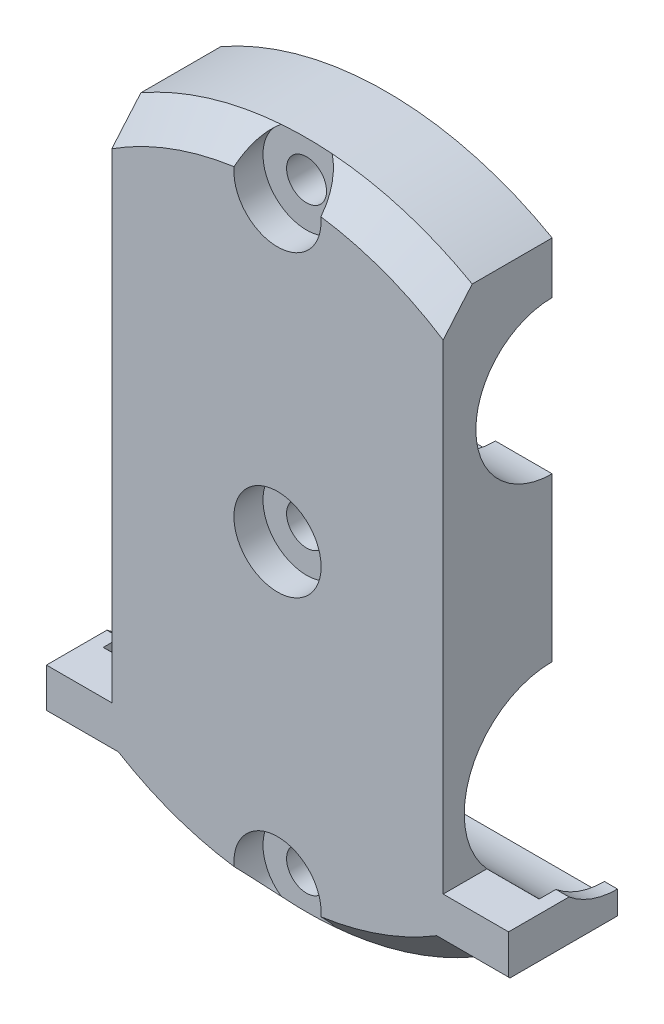
SolidWorks part; units mm, degrees
ref_plane "Front Plane" through (0, 0, 0) normal (0, 0, 1) x (1, 0, 0)
ref_plane "Top Plane" through (0, 0, 0) normal (0, 1, 0) x (1, 0, 0)
ref_plane "Right Plane" through (0, 0, 0) normal (1, 0, 0) x (0, 0, -1)
sketch "Sketch1" plane through (0, 0, 0) normal (0, 0, 1) x (1, 0, 0)
  line L15 (-23, -30.3987) -> (-32, -30.3987)
  line L16 (32, -39.9987) -> (23, -39.9987)
  line L17 (32, -39.9987) -> (32, -30.3987)
  line L18 (32, -30.3987) -> (23, -30.3987)
  line L19 (-32, -39.9987) -> (-32, -30.3987)
  line L21 (-23, -39.9987) -> (-32, -39.9987)
  line L23 (23, 39.9987) -> (23, -30.3987)
  line L25 (-23, 39.9987) -> (-23, -30.3987)
  arc A3 (23, 39.9987) -> (-23, 39.9987) centre (0, 0) ccw
  arc A4 (-23, -39.9987) -> (23, -39.9987) centre (0, 0) ccw
  point P3 (0, -32.9718)
  dimension "D1" = 92.28
  dimension "D2" = 9.6
  dimension "D3" = 64
  dimension "D4" = 46
  dimension "D5" = 9
  dimension "D6" = 9
extrude "Boss-Extrude1" add sketch "Sketch1" along normal blind 15
sketch "Sketch7" plane through (-23, 0, 0) normal (-1, 0, 0) x (0, 0, 1)
  line L0 (0, 39.9987) -> (0, -30.3987) construction
  line L1 (15, 39.9987) -> (0, 39.9987) construction
  circle A0 centre (0, 22.4987) radius 12.1
  dimension "D1" = 24.2
  dimension "D2" = 17.5
extrude "Cut-Extrude3" cut sketch "Sketch7" against normal blind 71.5
sketch "Sketch8" plane through (-23, 0, 0) normal (-1, 0, 0) x (0, 0, 1)
  line L0 (0, 10.3987) -> (0, -30.3987) construction
  line L1 (15, -39.9987) -> (0, -39.9987) construction
  circle A0 centre (0, -22.4987) radius 12.1
  dimension "D1" = 24.2
  dimension "D2" = 17.5
extrude "Cut-Extrude4" cut sketch "Sketch8" against normal blind 71.5 and the other way blind 71.5
sketch "Sketch9" plane through (-23, 0, 0) normal (-1, 0, 0) x (0, 0, 1)
  line L0 (0, 34.5987) -> (0, 32.9987)
  line L1 (0, 11.9987) -> (0, 10.3987)
  arc A0 (0, 11.9987) -> (0, 32.9987) centre (0, 22.4987) ccw
  arc A1 (0, 10.3987) -> (0, 34.5987) centre (0, 22.4987) ccw
  dimension "D1" = 21
extrude "Boss-Extrude4" add sketch "Sketch9" against normal blind 8
sketch "Sketch10" plane through (-32, 0, 0) normal (-1, 0, 0) x (0, 0, 1)
  line L1 (0, -32.9987) -> (0, -34.5987)
  line L2 (9.1652, -30.3987) -> (6.9166, -30.3987)
  arc A0 (0, -34.5987) -> (9.1652, -30.3987) centre (0, -22.4987) ccw
  arc A1 (0, -32.9987) -> (6.9166, -30.3987) centre (0, -22.4987) ccw
  dimension "D1" = 21
extrude "Boss-Extrude5" add sketch "Sketch10" against normal blind 2
mirror "Mirror1" about plane through (0, 0, 0) normal (1, 0, 0) of "Boss-Extrude5", "Boss-Extrude4"
sketch "Sketch11" plane through (0, 0, 0) normal (0, 0, -1) x (-1, 0, 0)
  circle A0 centre (0, 0) radius 2.75
  circle A1 centre (0, 41.1411) radius 2.75
  circle A2 centre (0, -41.1411) radius 2.75
extrude "Cut-Extrude5" cut sketch "Sketch11" against normal blind 24
sketch "Sketch12" plane through (0, 0, 15) normal (0, 0, 1) x (1, 0, 0)
  circle A0 centre (0, 0) radius 6
  circle A1 centre (0, -41.1411) radius 6
  circle A2 centre (0, 41.1411) radius 6
  dimension "D1" = 12
  dimension "D2" = 12
  dimension "D3" = 12
extrude "Cut-Extrude6" cut sketch "Sketch12" against normal blind 4
chamfer "Chamfer1" distance 4 angle 45 8 edges at (-13.5918, 44.0927, 15) (13.5918, 44.0927, 15) (13.5918, -44.0927, 15) (27.5, -39.9987, 15) (32, -39.9987, 7.5) (-13.5918, -44.0927, 15) (-27.5, -39.9987, 15) (-32, -39.9987, 7.5)
sketch "Sketch13" plane through (0, 0, 15) normal (0, 0, 1) x (1, 0, 0)
  line L0 (31.8, -38.312) -> (31.8, -30.5987)
  line L1 (31.8, -30.5987) -> (22.8, -30.5987)
  line L2 (22.8, -30.5987) -> (22.8, 43.8891)
  line L3 (22.8, 43.8891) -> (37.2276, 33.5836)
  line L4 (37.2276, 33.5836) -> (38.5613, -37.2208)
  line L5 (38.5613, -37.2208) -> (31.8, -38.312)
  line L6 (32, -35.9987) -> (32, -30.3987) construction
  line L7 (32, -30.3987) -> (23, -30.3987) construction
  line L8 (23, -30.3987) -> (23, 35.3098) construction
  line L9 (0, 0) -> (0, -50000) construction
  line L10 (-37.2276, 33.5836) -> (-38.5613, -37.2208)
  line L11 (-22.8, 43.8891) -> (-37.2276, 33.5836)
  line L12 (-22.8, -30.5987) -> (-22.8, 43.8891)
  line L13 (-31.8, -30.5987) -> (-22.8, -30.5987)
  line L14 (-31.8, -38.312) -> (-31.8, -30.5987)
  line L15 (-38.5613, -37.2208) -> (-31.8, -38.312)
  dimension "D1" = 0.2
  dimension "D2" = 0.2
  dimension "D3" = 0.2
extrude "Cut-Extrude7" cut sketch "Sketch13" against normal blind 28
